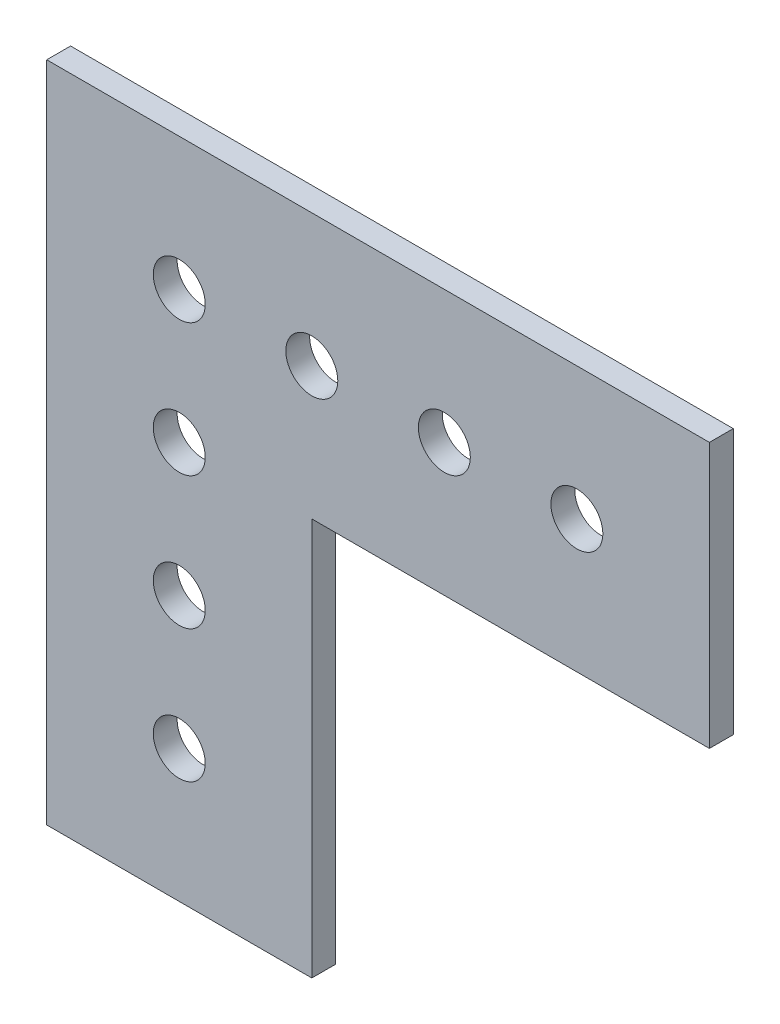
SolidWorks part; units mm, degrees
ref_plane "Front Plane" through (0, 0, 0) normal (0, 0, 1) x (1, 0, 0)
ref_plane "Top Plane" through (0, 0, 0) normal (0, 1, 0) x (1, 0, 0)
ref_plane "Right Plane" through (0, 0, 0) normal (1, 0, 0) x (0, 0, -1)
ref_plane "Plane1" through (0, 0, 0) normal (0, 0, -1) x (-1, 0, 0)
sketch "Sketch1" plane through (0, 0, 0) normal (0, 0, -1) x (-1, 0, 0)
  line L0 (12.7, 12.7) -> (-50.8, 12.7)
  line L2 (-50.8, 12.7) -> (-50.8, -12.7)
  line L4 (-50.8, -12.7) -> (-12.7, -12.7)
  line L5 (-12.7, -12.7) -> (-12.7, -50.8)
  line L7 (-12.7, -50.8) -> (12.7, -50.8)
  line L9 (12.7, -50.8) -> (12.7, 12.7)
  line L11 (0, 0) -> (-50.8, 0) construction
  line L12 (0, 0) -> (0, -50.8) construction
  circle A2 centre (0, -25.4) radius 2.4892
  circle A3 centre (-38.1, 0) radius 2.4892
  circle A4 centre (-12.7, 0) radius 2.4892
  circle A5 centre (0, 0) radius 2.4892
  circle A6 centre (-25.4, 0) radius 2.4892
  circle A7 centre (0, -12.7) radius 2.4892
  circle A8 centre (0, -38.1) radius 2.4892
  point P0 (-50.8, -6.35)
  point P1 (-50.8, 0)
  point P4 (0, -50.8)
  point P13 (0, 0)
  point P14 (0, -24.2765)
  point P29 (0, -38.0528)
  point P30 (0, 0)
  dimension "D3" = 12.7
  dimension "D9" = 4.9784
  dimension "D2" = 12.7
  dimension "D4" = 12.7
  dimension "D5" = 12.7
  dimension "D6" = 12.7
  dimension "D7" = 12.7
  dimension "D8" = 12.7
  dimension "D11" = 12.7
  dimension "D12" = 12.7
extrude "Boss-Extrude1" add sketch "Sketch1" against normal blind 2.286
equation "\"Thick\"= \"in\""
